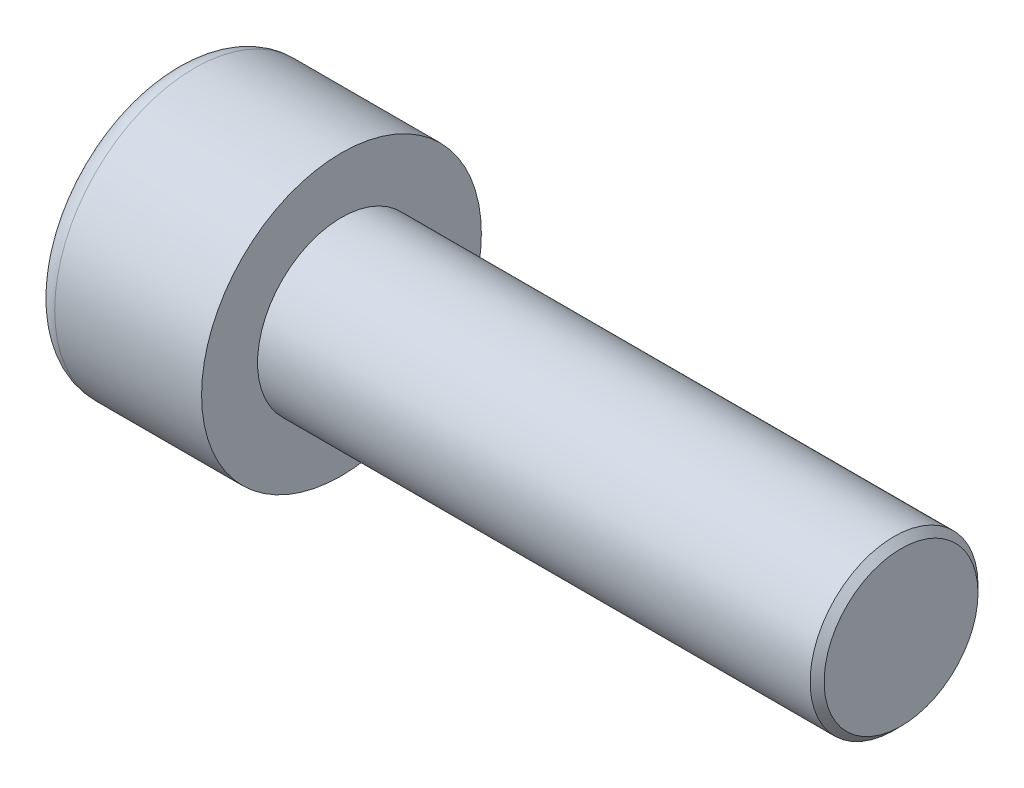
SolidWorks part; units mm, degrees
ref_plane "Front" through (0, 0, 0) normal (0, 0, 1) x (1, 0, 0)
ref_plane "Top" through (0, 0, 0) normal (0, 1, 0) x (1, 0, 0)
ref_plane "Right" through (0, 0, 0) normal (1, 0, 0) x (0, 0, -1)
sketch "Sketch1" plane through (0, 0, 0) normal (1, 0, 0) x (0, 0, -1)
  circle A0 centre (0, 0) radius 5
  dimension "dk" = 10
extrude "BaseHead" add sketch "Sketch1" along normal blind 6
sketch "Sketch2" plane through (6, 0, 0) normal (1, 0, 0) x (0, 0, -1)
  circle A0 centre (0, 0) radius 3
  dimension "d" = 6
extrude "BaseBody" add sketch "Sketch2" along normal blind 20
cosmetic thread "ThreadCosmetic1" parameters "b"=20, "D2"=4.917
sketch "Sketch3" plane through (0, 0, 0) normal (1, 0, 0) x (0, 0, -1)
  line L1 (2.8868, 0) -> (1.4434, 2.5)
  line L2 (1.4434, 2.5) -> (-1.4434, 2.5)
  line L3 (-1.4434, 2.5) -> (-2.8868, 0)
  line L4 (-2.8868, 0) -> (-1.4434, -2.5)
  line L5 (-1.4434, -2.5) -> (1.4434, -2.5)
  line L6 (1.4434, -2.5) -> (2.8868, 0)
  circle A0 centre (0, 0) radius 2.5 construction
  dimension "s" = 5
  dimension "e" = 5.7735
extrude "HexagonSocket" cut sketch "Sketch3" along normal blind 3
sketch "Sketch4" plane through (-4.1961, 0.75, 0) normal (0, 0, 1) x (-1, 0, 0)
  line L0 (-7.1961, 3.25) -> (-8.6395, 0.75)
  line L2 (-8.6395, 0.75) -> (-7.1961, 0.75)
  line L3 (-7.1961, 0.75) -> (-7.1961, 3.25)
  line L4 (-5.0351, 0.75) -> (0.839, 0.75) construction
  line L5 (-30.1961, 0.75) -> (-10.1961, 0.75) construction
  line L6 (-10.1961, 0.75) -> (-4.1961, 0.75) construction
  dimension "m" = 60
revolve "Cut-Revolve1" cut sketch "Sketch4" angle 360 about L4
fillet "HeadFillet" [suppressed] radius 0.25
fillet "TopFillet" radius 0.75 1 edges at (0, 0, -5)
chamfer "Chamfer1" distance 0.25 angle 45 1 edges at (26, 0, -3)
sketch "Sketch5" plane through (0, 0, 0) normal (0, 0, 1) x (1, 0, 0)
  line L0 (25.75, 2.531) -> (26.0208, 3)
  line L1 (26.0208, 3) -> (26.0208, 3.5415)
  line L2 (26.0208, 3.5415) -> (25.4793, 3.5415)
  line L3 (25.4793, 3.5415) -> (25.4793, 3)
  line L4 (25.4793, 3) -> (25.75, 2.531)
  line L5 (0, 0) -> (7.8886, 0) construction
  line L6 (25.75, -3) -> (25.75, 3) construction
  dimension "D1" = 6
  dimension "D2" = 0.5415
revolve "Cut-Revolve10" [suppressed] cut sketch "Sketch5" angle 360 about L5
pattern_linear "LPattern10" [suppressed] count 31 spacing 0.6498 along (1, 0, 0)
equation "\"r1@TopFillet\" = \"d@Sketch2\" / 8"
equation "\"D1@Chamfer1\" = \"r@HeadFillet\""
equation "\"D1@Sketch5\" = \"d@Sketch2\""
equation "\"D2@Sketch5\" =  ( \"d@Sketch2\" - \"D2@ThreadCosmetic1\" )  / 2"
equation "\"D3@LPattern10\" = \"D2@Sketch5\" * 1.2"
equation "\"D1@LPattern10\" = \"b@ThreadCosmetic1\" / \"D3@LPattern10\""
